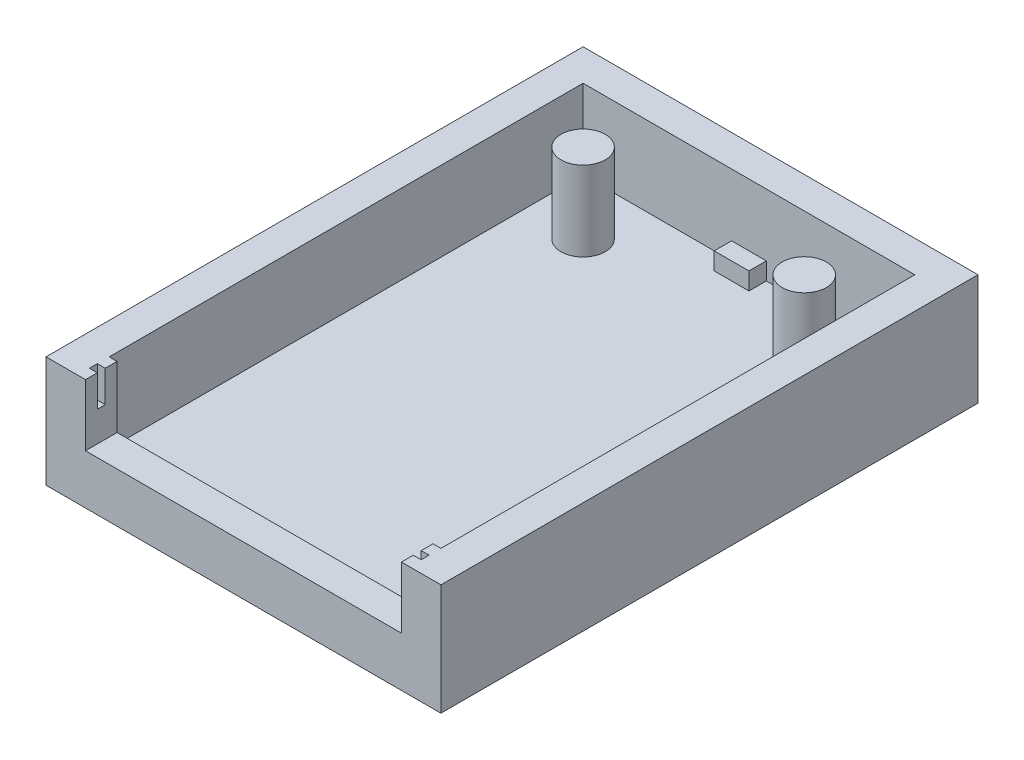
SolidWorks part; units mm, degrees
ref_plane "Ön Düzlem" through (0, 0, 0) normal (0, 0, 1) x (1, 0, 0)
ref_plane "Üst Düzlem" through (0, 0, 0) normal (0, 1, 0) x (1, 0, 0)
ref_plane "Sağ Düzlem" through (0, 0, 0) normal (1, 0, 0) x (0, 0, -1)
sketch "Çizim1" plane through (0, 0, 0) normal (0, 1, 0) x (1, 0, 0)
  line L1 (-12.5, 17) -> (12.5, 17)
  line L2 (-12.5, 17) -> (-12.5, -17)
  line L3 (-12.5, -17) -> (12.5, -17)
  line L4 (12.5, 17) -> (12.5, -17)
  line L5 (-12.5, 17) -> (12.5, -17) construction
  line L6 (-12.5, -17) -> (12.5, 17) construction
  point P0 (0, 0)
  dimension "D1" = 25
  dimension "D2" = 34
extrude "Yükseklik-Ekstrüzyon1" add sketch "Çizim1" along normal blind 7.04
sketch "Çizim2" plane through (0, 7.04, 0) normal (0, 1, 0) x (1, 0, 0)
  line L0 (-12.5, 17) -> (-12.5, -17) construction
  line L1 (-10.5, 15) -> (10.5, 15)
  line L2 (-10.5, 15) -> (-10.5, -15)
  line L3 (-10.5, -15) -> (10.5, -15)
  line L4 (10.5, 15) -> (10.5, -15)
  line L5 (-10.5, 15) -> (10.5, -15) construction
  line L6 (-10.5, -15) -> (10.5, 15) construction
  line L7 (12.5, 17) -> (-12.5, 17) construction
  circle A0 centre (-7, 11.5) radius 1.4
  circle A1 centre (7, 11.5) radius 1.4
  point P0 (0, 0)
  dimension "D6" = 2.8
  dimension "D1" = 2
  dimension "D2" = 2
  dimension "D3" = 3.5
  dimension "D4" = 3.5
  dimension "D5" = 3.5
extrude "Kes-Ekstrüzyon1" cut sketch "Çizim2" against normal blind 5.04
sketch "Çizim3" plane through (0, 7.04, 0) normal (0, 1, 0) x (1, 0, 0)
  line L1 (-10, -11.9633) -> (10, -11.9633)
  line L2 (-10, -11.9633) -> (-10, -17.6518)
  line L3 (-10, -17.6518) -> (10, -17.6518)
  line L4 (10, -11.9633) -> (10, -17.6518)
  line L5 (-10, -11.9633) -> (10, -17.6518) construction
  line L6 (-10, -17.6518) -> (10, -11.9633) construction
  point P0 (0, -14.8075)
  dimension "D1" = 20
extrude "Kes-Ekstrüzyon2" cut sketch "Çizim3" against normal blind 3.9
sketch "Çizim4" plane through (0, 2, 0) normal (0, 1, 0) x (1, 0, 0)
  line L0 (10.5, 15) -> (-10.5, 15) construction
  line L1 (-1.1, 15) -> (1.1, 15)
  line L2 (-1.1, 15) -> (-1.1, 13.9)
  line L3 (-1.1, 13.9) -> (1.1, 13.9)
  line L4 (1.1, 15) -> (1.1, 13.9)
  point P6 (0, 13.9)
  dimension "D1" = 1.1
  dimension "D2" = 2.2
extrude "Yükseklik-Ekstrüzyon2" add sketch "Çizim4" along normal blind 1.1
sketch "Çizim5" plane through (0, 7.04, 0) normal (0, 1, 0) x (1, 0, 0)
  line L0 (-10, -15) -> (-10, -17) construction
  line L1 (-10.5, -15.75) -> (-9.5, -15.75)
  line L2 (-10.5, -15.75) -> (-10.5, -16.25)
  line L3 (-10.5, -16.25) -> (-9.5, -16.25)
  line L4 (-9.5, -15.75) -> (-9.5, -16.25)
  line L5 (-10.5, -15.75) -> (-9.5, -16.25) construction
  line L6 (-10.5, -16.25) -> (-9.5, -15.75) construction
  line L7 (10, -17) -> (10, -15) construction
  line L8 (9.5, -15.75) -> (10.5, -15.75)
  line L9 (9.5, -15.75) -> (9.5, -16.25)
  line L10 (9.5, -16.25) -> (10.5, -16.25)
  line L11 (10.5, -15.75) -> (10.5, -16.25)
  line L12 (9.5, -15.75) -> (10.5, -16.25) construction
  line L13 (9.5, -16.25) -> (10.5, -15.75) construction
  point P0 (-10, -16)
  point P7 (10, -16)
  dimension "D1" = 0.5
  dimension "D2" = 1
extrude "Kes-Ekstrüzyon3" cut sketch "Çizim5" against normal blind 2
